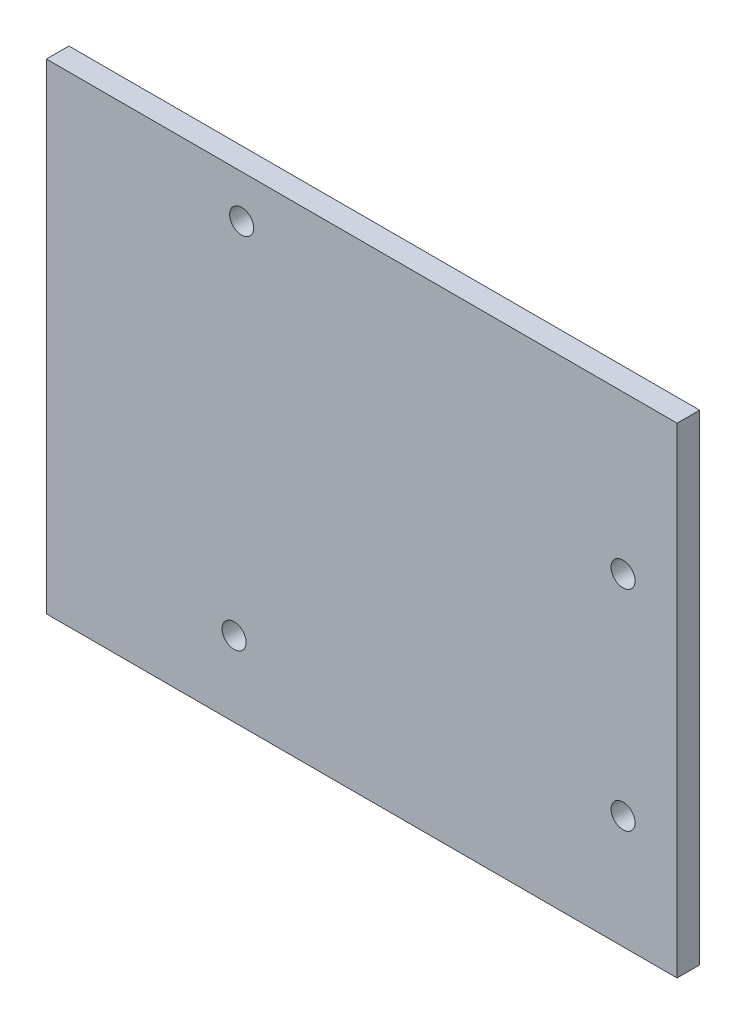
SolidWorks part; units mm, degrees
ref_plane "Front Plane" through (0, 0, 0) normal (0, 0, 1) x (1, 0, 0)
ref_plane "Top Plane" through (0, 0, 0) normal (0, 1, 0) x (1, 0, 0)
ref_plane "Right Plane" through (0, 0, 0) normal (1, 0, 0) x (0, 0, -1)
sketch "Sketch1" plane through (0, 0, 0) normal (0, 0, 1) x (1, 0, 0)
  line L1 (-50, 50) -> (50, 50)
  line L2 (-50, 50) -> (-50, -50)
  line L3 (-50, -50) -> (50, -50)
  line L4 (50, 50) -> (50, -50)
  line L5 (-50, 50) -> (50, -50) construction
  line L6 (-50, -50) -> (50, 50) construction
  point P0 (0, 0)
  point P6 (0, 50)
  dimension "D1" = 100
  dimension "D2" = 100
extrude "Boss-Extrude1" add sketch "Sketch1" along normal blind 3
sketch "Sketch2" plane through (0, 0, 3) normal (0, 0, 1) x (1, 0, 0)
  line L2 (-25.5925, 8.2895) -> (-25, -40) construction
  line L3 (-50, 50) -> (-50, -50) construction
  line L4 (-50, -50) -> (50, -50) construction
  circle A0 centre (26.8075, -34.9) radius 1.6
  circle A1 centre (26.8075, -7) radius 1.6
  circle A2 centre (-25, -40) radius 1.6
  circle A3 centre (-23.9925, 8.2895) radius 1.6
  dimension "D3" = 3.2
  dimension "D1" = 27.9
  dimension "D2" = 48.3
  dimension "D4" = 5.1
  dimension "D5" = 25
  dimension "D6" = 50.8
  dimension "D7" = 10
extrude "Cut-Extrude1" cut sketch "Sketch2" against normal blind 59
sketch "Sketch3" plane through (0, 0, 3) normal (0, 0, 1) x (1, 0, 0)
  line L0 (-50, 14) -> (34, 14)
  line L1 (-50, 50) -> (-50, -50) construction
  line L2 (34, 14) -> (34, -50)
  line L3 (-50, -50) -> (50, -50) construction
  line L4 (34, -50) -> (50, -50)
  line L5 (50, -50) -> (50, 50)
  line L6 (50, 50) -> (-50, 50)
  line L7 (-50, 50) -> (-50, 14)
  dimension "D1" = 64
  dimension "D2" = 84
extrude "Cut-Extrude2" cut sketch "Sketch3" against normal blind 3
